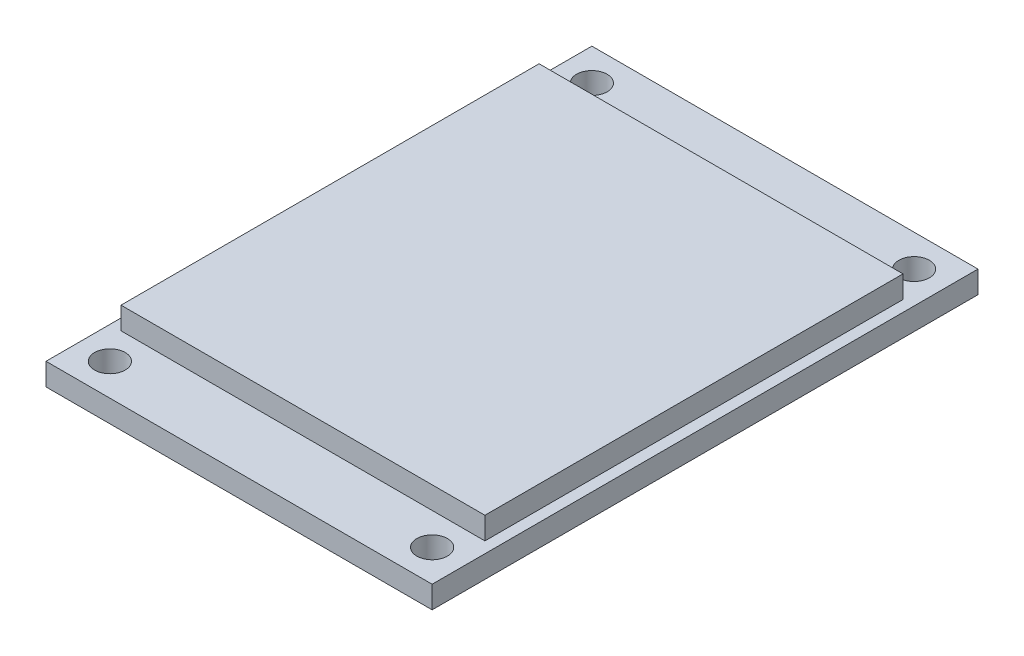
SolidWorks part; units mm, degrees
ref_plane "前视基准面" through (0, 0, 0) normal (0, 0, 1) x (1, 0, 0)
ref_plane "上视基准面" through (0, 0, 0) normal (0, 1, 0) x (1, 0, 0)
ref_plane "右视基准面" through (0, 0, 0) normal (1, 0, 0) x (0, 0, -1)
sketch "草图1" plane through (0, 0, 0) normal (0, 1, 0) x (1, 0, 0)
  line L1 (13.9, -19.65) -> (-13.9, -19.65)
  line L2 (13.9, -19.65) -> (13.9, 19.65)
  line L3 (13.9, 19.65) -> (-13.9, 19.65)
  line L4 (-13.9, -19.65) -> (-13.9, 19.65)
  line L5 (13.9, -19.65) -> (-13.9, 19.65) construction
  line L6 (13.9, 19.65) -> (-13.9, -19.65) construction
  point P0 (0, 0)
  dimension "D1" = 27.8
  dimension "D2" = 39.3
extrude "凸台-拉伸1" add sketch "草图1" along normal blind 1.6
sketch "草图2" plane through (0, 1.6, 0) normal (0, 1, 0) x (1, 0, 0)
  line L0 (13.9, 19.65) -> (-13.9, 19.65) construction
  line L1 (-13.9, 19.65) -> (-13.9, -19.65) construction
  line L2 (0, -0.88) -> (0, 0.88) construction
  line L3 (-0.88, 0) -> (0.88, 0) construction
  circle A0 centre (-11.6, 17.35) radius 1.1
  circle A2 centre (11.6, 17.35) radius 1.1
  circle A3 centre (-11.6, -17.35) radius 1.1
  circle A4 centre (11.6, -17.35) radius 1.1
  point P2 (-11.6, 18.45)
  point P3 (-12.7, 17.35)
  dimension "D1" = 2.2
  dimension "D2" = 1.2
  dimension "D3" = 1.2
extrude "切除-拉伸1" cut sketch "草图2" against normal blind 1.6
sketch "草图3" plane through (0, 1.6, 0) normal (0, 1, 0) x (1, 0, 0)
  line L0 (13.9, 19.65) -> (-13.9, 19.65) construction
  line L1 (-13.1, -15.05) -> (13.1, -15.05)
  line L2 (-13.1, -15.05) -> (-13.1, 15.05)
  line L3 (-13.1, 15.05) -> (13.1, 15.05)
  line L4 (13.1, -15.05) -> (13.1, 15.05)
  line L5 (-13.1, -15.05) -> (13.1, 15.05) construction
  line L6 (-13.1, 15.05) -> (13.1, -15.05) construction
  point P0 (0, 0)
  dimension "D1" = 26.2
  dimension "D2" = 4.6
extrude "凸台-拉伸2" add sketch "草图3" along normal blind 1.6
sketch "草图4" plane through (0, 0, 0) normal (0, -1, 0) x (1, 0, 0)
  line L0 (13.9, -19.65) -> (-13.9, -19.65) construction
  line L1 (8.89, -18.95) -> (-8.89, -18.95)
  line L2 (8.89, -18.95) -> (8.89, -16.41)
  line L3 (8.89, -16.41) -> (-8.89, -16.41)
  line L4 (-8.89, -18.95) -> (-8.89, -16.41)
  line L5 (8.89, -18.95) -> (-8.89, -16.41) construction
  line L6 (8.89, -16.41) -> (-8.89, -18.95) construction
  point P0 (0, -17.68)
  point P5 (0, 0)
  dimension "D1" = 2.54
  dimension "D2" = 17.78
  dimension "D3" = 0.7
extrude "凸台-拉伸3" add sketch "草图4" along normal blind 2.54
